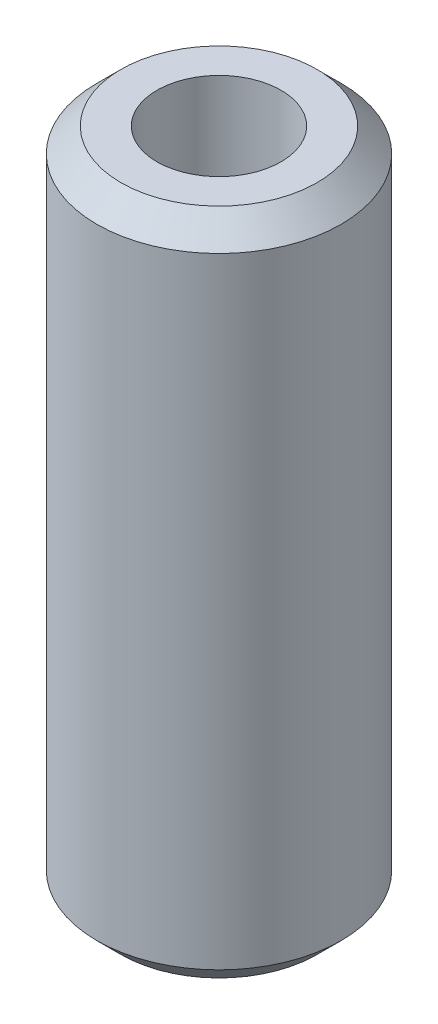
SolidWorks part; units mm, degrees
ref_plane "Front Plane" through (0, 0, 0) normal (0, 0, 1) x (1, 0, 0)
ref_plane "Top Plane" through (0, 0, 0) normal (0, 1, 0) x (1, 0, 0)
ref_plane "Right Plane" through (0, 0, 0) normal (1, 0, 0) x (0, 0, -1)
sketch "Sketch1" plane through (0, 0, 0) normal (0, 0, 1) x (1, 0, 0)
  line L0 (0, 78.8082) -> (0, -73.3637) construction
  line L1 (12.7, 32.25) -> (12.7, -32.25)
  line L3 (6.45, 34.75) -> (6.45, -34.75)
  line L4 (-34.1638, 0) -> (81.8026, 0) construction
  line L6 (12.7, 32.25) -> (10.2, 34.75)
  line L7 (10.2, 34.75) -> (6.45, 34.75)
  line L8 (12.7, -32.25) -> (10.2, -34.75)
  line L9 (10.2, -34.75) -> (6.45, -34.75)
  point P5 (12.7, 0)
  dimension "D1" = 2.5
  dimension "D2" = 12.7
  dimension "D3" = 6.45
  dimension "D4" = 69.5
  dimension "D5" = 45
revolve "Revolve1" add sketch "Sketch1" angle 360 about L0
